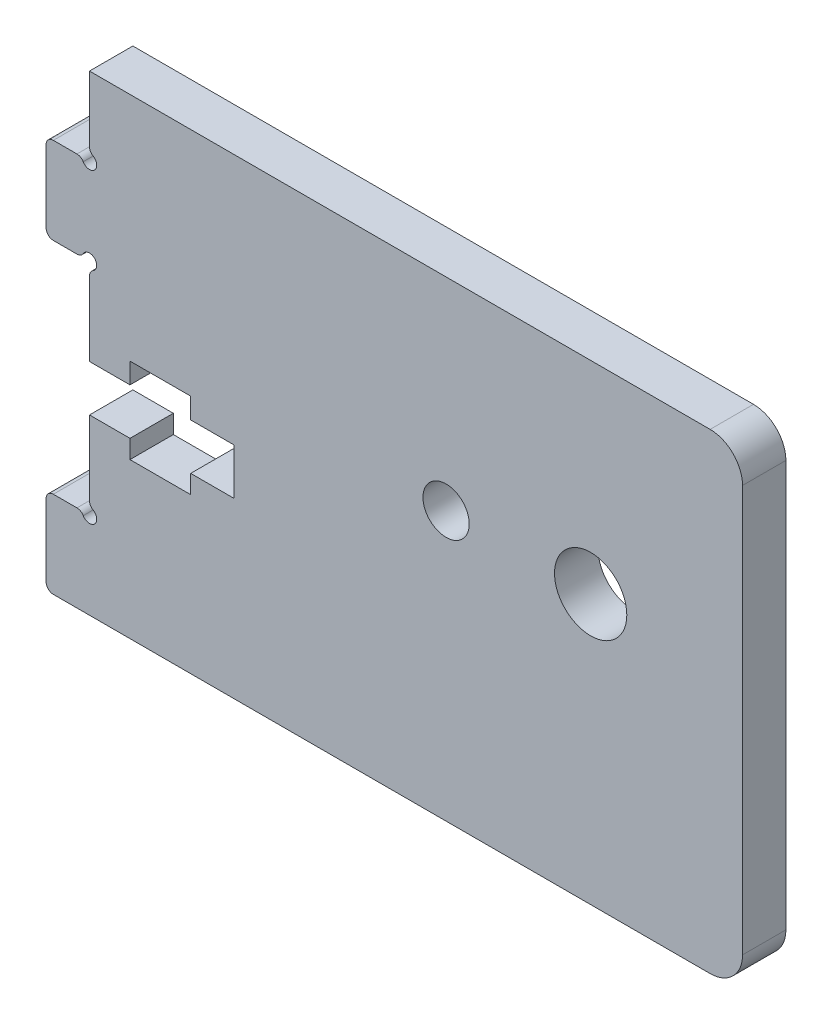
SolidWorks part; units mm, degrees
ref_plane "Front Plane" through (0, 0, 0) normal (0, 0, 1) x (1, 0, 0)
ref_plane "Top Plane" through (0, 0, 0) normal (0, 1, 0) x (1, 0, 0)
ref_plane "Right Plane" through (0, 0, 0) normal (1, 0, 0) x (0, 0, -1)
sketch "Model" plane through (0, 0, 0) normal (0, 0, 1) x (1, 0, 0)
  line L0 (146.0201, 163.9297) -> (146.0201, 158.9297)
  line L1 (149.0201, 170.4297) -> (149.0201, 165.2957)
  line L2 (151.8201, 170.4297) -> (149.0201, 170.4297)
  line L3 (151.8201, 169.1547) -> (151.8201, 170.4297)
  line L4 (156.0201, 169.1547) -> (151.8201, 169.1547)
  line L5 (156.0201, 170.4297) -> (156.0201, 169.1547)
  line L6 (159.0201, 170.4297) -> (156.0201, 170.4297)
  line L7 (159.0201, 173.6297) -> (159.0201, 170.4297)
  line L8 (156.0202, 173.6297) -> (159.0201, 173.6297)
  line L9 (156.0202, 175.0547) -> (156.0202, 173.6297)
  line L10 (151.8202, 175.0547) -> (156.0202, 175.0547)
  line L11 (151.8202, 173.6297) -> (151.8202, 175.0547)
  line L12 (149.0202, 173.6297) -> (151.8202, 173.6297)
  line L13 (149.0202, 178.7637) -> (149.0202, 173.6297)
  line L14 (146.0201, 185.1297) -> (146.0201, 180.1297)
  line L15 (148.1541, 185.6297) -> (146.5201, 185.6297)
  line L16 (149.0202, 191.0297) -> (149.0202, 186.4957)
  line L17 (191.9494, 191.0297) -> (149.0202, 191.0297)
  line L18 (146.5201, 158.4297) -> (191.9494, 158.4297)
  line L19 (194.1894, 188.7897) -> (194.1894, 160.6697)
  line L20 (146.5201, 179.6297) -> (148.1541, 179.6297)
  line L21 (146.5201, 164.4297) -> (148.1541, 164.4297)
  arc A0 (146.0201, 158.9297) -> (146.5201, 158.4297) centre (146.5201, 158.9297) ccw
  arc A1 (148.5871, 164.1797) -> (149.2701, 164.8627) centre (149.0201, 164.4297) ccw
  arc A2 (149.0201, 165.2957) -> (149.2701, 164.8627) centre (149.5201, 165.2957) ccw
  arc A3 (149.2702, 179.1967) -> (149.0202, 178.7637) centre (149.5202, 178.7637) ccw
  arc A4 (149.2702, 179.1967) -> (148.5872, 179.8797) centre (149.0202, 179.6297) ccw
  arc A5 (146.5201, 185.6297) -> (146.0201, 185.1297) centre (146.5201, 185.1297) ccw
  arc A6 (148.5872, 185.3797) -> (148.1541, 185.6297) centre (148.1541, 185.1297) ccw
  arc A7 (148.5872, 185.3797) -> (149.2702, 186.0627) centre (149.0202, 185.6297) ccw
  arc A8 (149.0202, 186.4957) -> (149.2702, 186.0627) centre (149.5202, 186.4957) ccw
  circle A9 centre (173.6854, 177.0297) radius 1.6
  circle A10 centre (183.6854, 177.0297) radius 2.5
  arc A11 (194.1894, 188.7897) -> (191.9494, 191.0297) centre (191.9494, 188.7897) ccw
  arc A12 (191.9494, 158.4297) -> (194.1894, 160.6697) centre (191.9494, 160.6697) ccw
  arc A13 (146.5201, 164.4297) -> (146.0201, 163.9297) centre (146.5201, 163.9297) ccw
  arc A14 (148.5871, 164.1797) -> (148.1541, 164.4297) centre (148.1541, 163.9297) ccw
  arc A15 (146.0201, 180.1297) -> (146.5201, 179.6297) centre (146.5201, 180.1297) ccw
  arc A16 (148.1541, 179.6297) -> (148.5872, 179.8797) centre (148.1541, 180.1297) ccw
extrude "Boss-Extrude1" add sketch "Model" along normal blind 3
